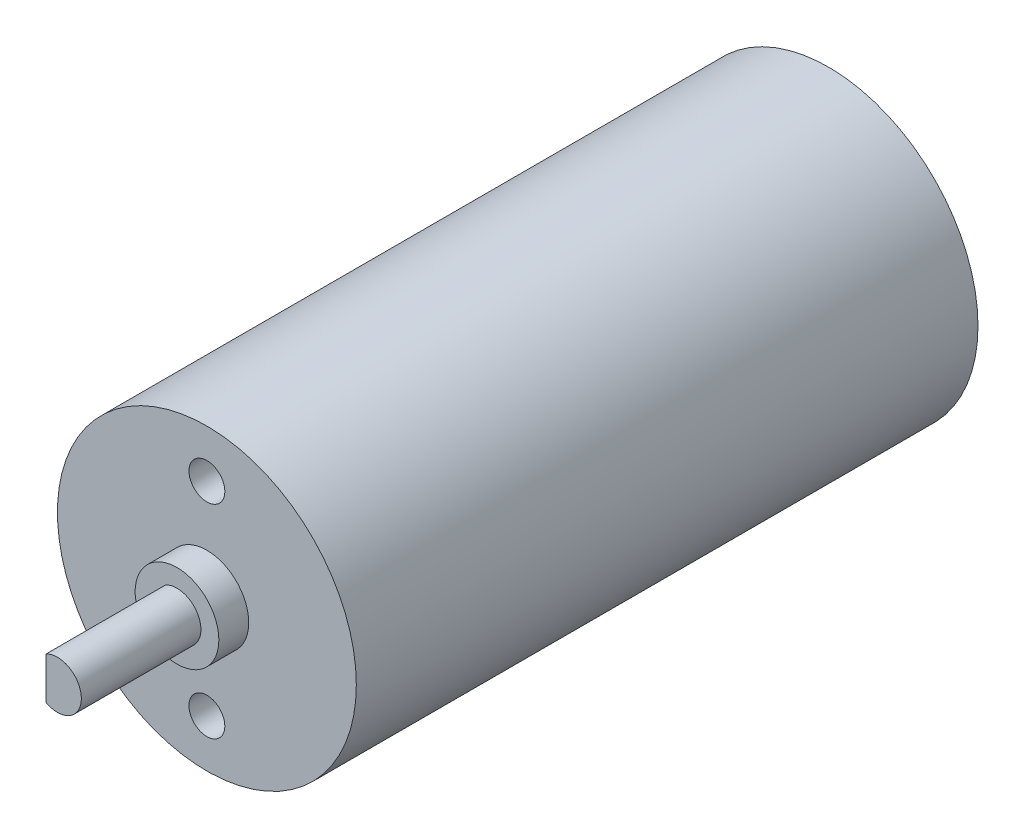
SolidWorks part; units mm, degrees
ref_plane "Front" through (0, 0, 0) normal (0, 0, 1) x (1, 0, 0)
ref_plane "Top" through (0, 0, 0) normal (0, 1, 0) x (1, 0, 0)
ref_plane "Right" through (0, 0, 0) normal (1, 0, 0) x (0, 0, -1)
sketch "草图1" plane through (0, 0, 0) normal (0, 0, 1) x (1, 0, 0)
  circle A0 centre (0, 0) radius 12.5
extrude "凸台-拉伸1" add sketch "草图1" along normal blind 52
sketch "草图2" plane through (0, 0, 52) normal (0, 0, 1) x (1, 0, 0)
  circle A0 centre (0, 0) radius 3.5
extrude "凸台-拉伸2" add sketch "草图2" along normal blind 2.5
sketch "草图3" plane through (0, 0, 54.5) normal (0, 0, 1) x (1, 0, 0)
  circle A0 centre (0, 0) radius 2
extrude "凸台-拉伸3" add sketch "草图3" along normal blind 10
sketch "草图4" plane through (0, 0, 64.5) normal (0, 0, 1) x (1, 0, 0)
  line L1 (-0.9579, -1.7557) -> (-0.9579, 1.7557)
  arc A1 (-0.9579, 1.7557) -> (-0.9579, -1.7557) centre (0, 0) ccw
extrude "切除-拉伸1" cut sketch "草图4" against normal blind 10
sketch "草图5" plane through (0, 0, 52) normal (0, 0, 1) x (1, 0, 0)
  circle A0 centre (0, 8.5) radius 1.5
  circle A1 centre (0, -8.5) radius 1.5
  dimension "D1" = 8.5
  dimension "D2" = 8.5
extrude "切除-拉伸2" cut sketch "草图5" against normal blind 7
